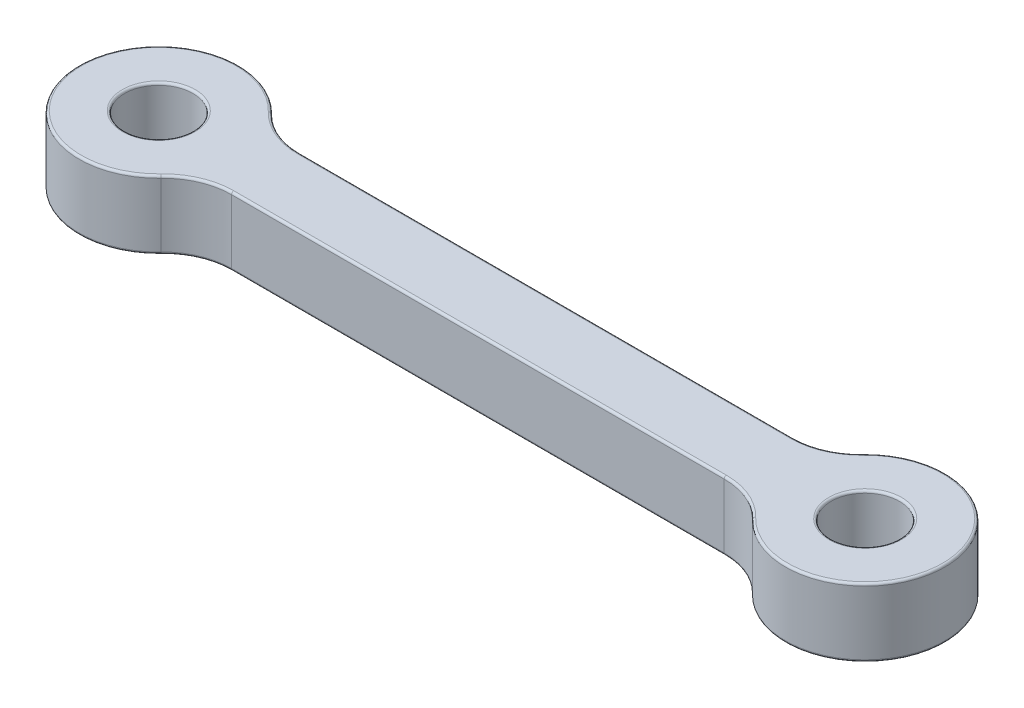
SolidWorks part; units mm, degrees
ref_plane "Front Plane" through (0, 0, 0) normal (0, 0, 1) x (1, 0, 0)
ref_plane "Top Plane" through (0, 0, 0) normal (0, 1, 0) x (1, 0, 0)
ref_plane "Right Plane" through (0, 0, 0) normal (1, 0, 0) x (0, 0, -1)
sketch "Sketch1" plane through (0, 0, 0) normal (0, 1, 0) x (1, 0, 0)
  line L0 (0, 0) -> (1.5, 0)
  line L1 (4.6904, 1.5) -> (26.3096, 1.5)
  line L2 (4.6904, -1.5) -> (26.3096, -1.5)
  line L3 (0, 1.5) -> (31, 1.5) construction
  line L5 (0, 0) -> (31, 0) construction
  line L6 (0, -1.5) -> (31, -1.5) construction
  arc A0 (2.5256, 2.4231) -> (2.5256, -2.4231) centre (0, 0) ccw
  circle A1 centre (0, 0) radius 1.5
  circle A2 centre (31, 0) radius 1.5
  arc A3 (28.4744, -2.4231) -> (28.4744, 2.4231) centre (31, 0) ccw
  arc A4 (28.4744, -2.4231) -> (26.3096, -1.5) centre (26.3096, -4.5) ccw
  arc A5 (26.3096, 1.5) -> (28.4744, 2.4231) centre (26.3096, 4.5) ccw
  arc A6 (4.6904, -1.5) -> (2.5256, -2.4231) centre (4.6904, -4.5) ccw
  arc A7 (4.6904, 1.5) -> (2.5256, 2.4231) centre (4.6904, 4.5) cw
  dimension "D1" = 7
  dimension "D2" = 3
  dimension "D4" = 7
  dimension "D5" = 3
  dimension "D8" = 3
  dimension "D3" = 31
  dimension "D6" = 1.5
  dimension "D7" = 1.5
extrude "Boss-Extrude1" add sketch "Sketch1" along normal blind 3 contours L1 A7 A0 A6 L2 A4 A3 A5 A1 A2
fillet "Fillet1" radius 0.1 20 edges at (3.5137, 0, -1.7404) (-3.5, 0, 0) (3.5137, 0, 1.7404) (15.5, 0, 1.5) (27.4863, 0, 1.7404) (34.5, 0, 0) (27.4863, 0, -1.7404) (15.5, 0, -1.5) (31, 0, 1.5) (0, 0, 1.5) (27.4863, 3, -1.7404) (34.5, 3, 0) (27.4863, 3, 1.7404) (15.5, 3, 1.5) (3.5137, 3, 1.7404) (-3.5, 3, 0) (3.5137, 3, -1.7404) (15.5, 3, -1.5) (31, 3, 1.5) (0, 3, 1.5)
